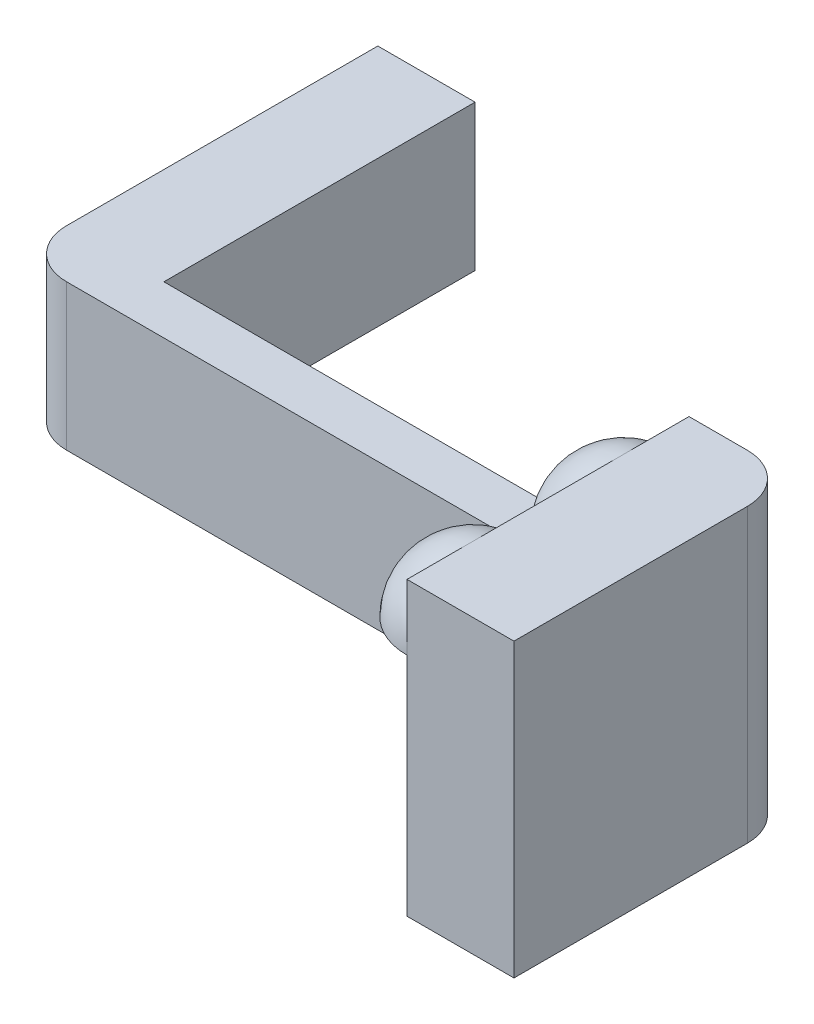
SolidWorks part; units mm, degrees
ref_plane "Front Plane" through (0, 0, 0) normal (0, 0, 1) x (1, 0, 0)
ref_plane "Top Plane" through (0, 0, 0) normal (0, 1, 0) x (1, 0, 0)
ref_plane "Right Plane" through (0, 0, 0) normal (1, 0, 0) x (0, 0, -1)
other "Configuration Table"
sketch "Sketch1" plane through (0, 0, 0) normal (0, 0, 1) x (1, 0, 0)
  line L1 (30, 7.5) -> (-30, 7.5)
  line L2 (30, 7.5) -> (30, -7.5)
  line L3 (30, -7.5) -> (-30, -7.5)
  line L4 (-30, 7.5) -> (-30, -7.5)
  line L5 (30, 7.5) -> (-30, -7.5) construction
  line L6 (30, -7.5) -> (-30, 7.5) construction
  point P0 (0, 0)
  dimension "D1" = 60
  dimension "D2" = 15
extrude "Boss-Extrude1" add sketch "Sketch1" along normal blind 5
sketch "Sketch2" plane through (-30, 0, 0) normal (-1, 0, 0) x (0, 0, 1)
  line L0 (5, -7.5) -> (0, -7.5) construction
  line L1 (5, 7.5) -> (-32, 7.5)
  line L2 (5, 7.5) -> (5, -7.5)
  line L3 (5, -7.5) -> (-32, -7.5)
  line L4 (-32, 7.5) -> (-32, -7.5)
  dimension "D1" = 37
extrude "Boss-Extrude2" add sketch "Sketch2" along normal blind 10
fillet "Fillet1" radius 5 1 edges at (-40, 0, 5)
sketch "Sketch3" plane through (30, 0, 0) normal (1, 0, 0) x (0, 0, -1)
  line L1 (0, 22.5) -> (-29, 22.5)
  line L2 (0, 22.5) -> (0, -7.5)
  line L3 (0, -7.5) -> (-29, -7.5)
  line L4 (-29, 22.5) -> (-29, -7.5)
  line L5 (-5, -7.5) -> (0, -7.5) construction
  line L6 (0, 13.6459) -> (0, -13.6459) construction
  dimension "D1" = 29
  dimension "D2" = 30
extrude "Boss-Extrude3" add sketch "Sketch3" along normal blind 5
fillet "Fillet2" radius 5 1 edges at (35, 7.5, 0)
sketch "Sketch8" plane through (0, 0, 5) normal (0, 0, 1) x (1, 0, 0)
  line L1 (35, 22.5) -> (30, 22.5) construction
  line L12 (30, -7.5) -> (30, 7.5) construction
  line L13 (30, 22.5) -> (24, 22.5)
  line L14 (30, 22.5) -> (30, -7.5)
  line L15 (30, -7.5) -> (24, -7.5)
  line L16 (24, 22.5) -> (24, -7.5)
  line L18 (-35, -7.5) -> (30, -7.5) construction
  line L19 (30, 22.5) -> (30, -7.5) construction
  dimension "D1" = 6
extrude "Boss-Extrude6" add sketch "Sketch8" along normal up to surface and the other way up to surface up to face at (32.5, 7.5, 29) other way up to face at (0, 0, 0)
sketch "Sketch7" plane through (0, -7.5, 0) normal (0, -1, 0) x (1, 0, 0)
  line L0 (35, 29) -> (35, 5) construction
  line L1 (33, 27) -> (27, 27)
  line L2 (33, 27) -> (33, 5)
  line L3 (33, 5) -> (27, 5)
  line L4 (27, 27) -> (27, 5)
  line L5 (33, 27) -> (27, 5) construction
  line L6 (33, 5) -> (27, 27) construction
  line L7 (13.6459, 0) -> (-13.6459, 0) construction
  line L8 (-40, -32) -> (-40, 0) construction
  line L9 (-32, -5) -> (-38, -5)
  line L10 (-32, -5) -> (-32, -27)
  line L11 (-32, -27) -> (-38, -27)
  line L12 (-38, -5) -> (-38, -27)
  line L13 (-32, -5) -> (-38, -27) construction
  line L14 (-32, -27) -> (-38, -5) construction
  line L15 (-40, -32) -> (-30, -32) construction
  point P0 (30, 16)
  point P9 (-35, -16)
  dimension "D1" = 22
  dimension "D2" = 6
  dimension "D3" = 2
  dimension "D4" = 5
  dimension "D5" = 2
  dimension "D6" = 5
extrude "Cut-Extrude3" cut sketch "Sketch7" against normal blind 11
sketch "Sketch9" plane through (24, 0, 0) normal (-1, 0, 0) x (0, 0, 1)
  line L0 (29, -7.5) -> (29, 22.5) construction
  line L1 (0, 22.5) -> (0, 7.5) construction
  line L2 (29, 22.5) -> (0, 22.5) construction
  line L3 (0, 15.75) -> (13.5, 15.75)
  line L4 (15.5, 15.75) -> (29, 15.75)
  arc A0 (13.5, 15.75) -> (0, 15.75) centre (6.75, 15.75) ccw
  arc A1 (29, 15.75) -> (15.5, 15.75) centre (22.25, 15.75) ccw
  dimension "D1" = 13.5
revolve "Revolve1" add sketch "Sketch9" angle 90 about L3
